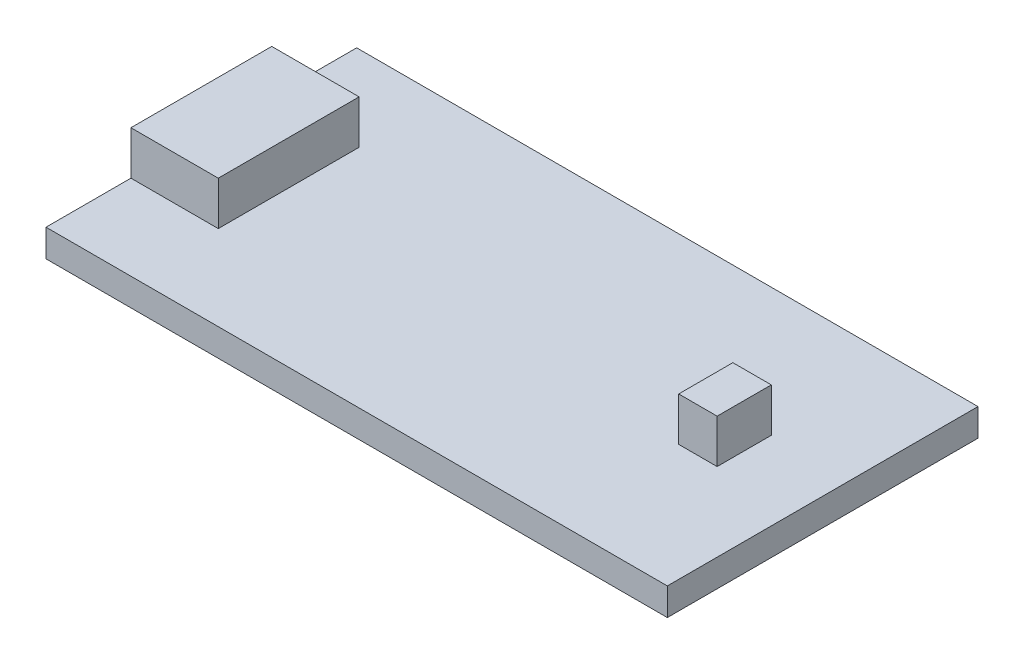
SolidWorks part; units mm, degrees
ref_plane "Front Plane" through (0, 0, 0) normal (0, 0, 1) x (1, 0, 0)
ref_plane "Top Plane" through (0, 0, 0) normal (0, 1, 0) x (1, 0, 0)
ref_plane "Right Plane" through (0, 0, 0) normal (1, 0, 0) x (0, 0, -1)
sketch "Sketch1" plane through (0, 0, 0) normal (0, 1, 0) x (1, 0, 0)
  line L1 (-17.78, 8.89) -> (17.78, 8.89)
  line L2 (-17.78, 8.89) -> (-17.78, -8.89)
  line L3 (-17.78, -8.89) -> (17.78, -8.89)
  line L4 (17.78, 8.89) -> (17.78, -8.89)
  line L5 (0, -8.89) -> (0, 8.89) construction
  line L6 (-17.78, 0) -> (17.78, 0) construction
  point P0 (0, 0)
  dimension "D1" = 35.56
  dimension "D2" = 17.78
extrude "Board" add sketch "Sketch1" along normal blind 1.57
sketch "Sketch2" plane through (0, 1.57, 0) normal (0, 1, 0) x (1, 0, 0)
  line L0 (-17.78, 8.89) -> (-17.78, -8.89) construction
  line L1 (-17.78, -4.03) -> (-12.78, -4.03)
  line L2 (-17.78, -4.03) -> (-17.78, 4.03)
  line L3 (-17.78, 4.03) -> (-12.78, 4.03)
  line L4 (-12.78, -4.03) -> (-12.78, 4.03)
  line L5 (-15.28, 4.03) -> (-15.28, -4.03) construction
  line L6 (-17.78, 0) -> (-12.78, 0) construction
  point P0 (-15.28, 0)
  dimension "D1" = 8.06
  dimension "D2" = 5
extrude "MicroUSB" add sketch "Sketch2" along normal blind 2.5
sketch "Sketch3" plane through (0, 1.57, 0) normal (0, 1, 0) x (1, 0, 0)
  line L0 (-17.78, 8.89) -> (-17.78, 4.03) construction
  line L1 (11.09, -1.55) -> (13.29, -1.55)
  line L2 (11.09, -1.55) -> (11.09, 1.55)
  line L3 (11.09, 1.55) -> (13.29, 1.55)
  line L4 (13.29, -1.55) -> (13.29, 1.55)
  line L5 (12.19, 1.55) -> (12.19, -1.55) construction
  line L6 (11.09, 0) -> (13.29, 0) construction
  point P0 (12.19, 0)
  dimension "D1" = 3.1
  dimension "D2" = 29.97
  dimension "D3" = 2.2
extrude "Button" add sketch "Sketch3" along normal blind 2.5
sketch "Sketch4" plane through (0, 0, 0) normal (0, 1, 0) x (1, 0, 0)
  line L0 (6.4, 8.89) -> (6.4, -8.89) construction
  line L1 (17.78, 8.89) -> (-17.78, 8.89) construction
  line L2 (-17.78, -8.89) -> (17.78, -8.89) construction
  line L3 (17.78, -8.89) -> (17.78, 8.89) construction
  line L4 (-5, 8.89) -> (-5, -8.89) construction
  line L6 (-5, -6.22) -> (6.4, -6.22) construction
  line L7 (-5, -6.22) -> (-5, 5.27) construction
  line L8 (-5, 5.27) -> (6.4, 5.27) construction
  line L9 (6.4, -6.22) -> (6.4, 5.27) construction
  line L10 (-4.0119, 4.9121) -> (-2.6232, 4.9121)
  line L11 (-4.0119, 4.9121) -> (-4.0119, 3.8319)
  line L12 (-4.0119, 3.8319) -> (-2.6232, 3.8319)
  line L13 (-2.6232, 4.9121) -> (-2.6232, 3.8319)
  line L14 (-4.0119, 4.9121) -> (-2.6232, 3.8319) construction
  line L15 (-4.0119, 3.8319) -> (-2.6232, 4.9121) construction
  line L16 (0.7458, 2.5975) -> (1.7745, 2.5975)
  line L17 (0.7458, 2.5975) -> (0.7458, 3.8319)
  line L18 (0.7458, 3.8319) -> (1.7745, 3.8319)
  line L19 (1.7745, 2.5975) -> (1.7745, 3.8319)
  line L20 (0.7458, 2.5975) -> (1.7745, 3.8319) construction
  line L21 (0.7458, 3.8319) -> (1.7745, 2.5975) construction
  line L22 (4.2434, 2.7775) -> (5.375, 2.7775)
  line L23 (4.2434, 2.7775) -> (4.2434, 4.372)
  line L24 (4.2434, 4.372) -> (5.375, 4.372)
  line L25 (5.375, 2.7775) -> (5.375, 4.372)
  line L26 (4.2434, 2.7775) -> (5.375, 4.372) construction
  line L27 (4.2434, 4.372) -> (5.375, 2.7775) construction
  line L28 (3.2404, 1.2344) -> (3.9605, 1.2344)
  line L29 (3.2404, 1.2344) -> (3.2404, -1.2344)
  line L30 (3.2404, -1.2344) -> (3.9605, -1.2344)
  line L31 (3.9605, 1.2344) -> (3.9605, -1.2344)
  line L32 (3.2404, 1.2344) -> (3.9605, -1.2344) construction
  line L33 (3.2404, -1.2344) -> (3.9605, 1.2344) construction
  line L34 (1.1316, -1.8517) -> (-0.6172, -1.8517)
  line L35 (1.1316, -1.8517) -> (1.1316, -3.7033)
  line L36 (1.1316, -3.7033) -> (-0.6172, -3.7033)
  line L37 (-0.6172, -1.8517) -> (-0.6172, -3.7033)
  line L38 (1.1316, -1.8517) -> (-0.6172, -3.7033) construction
  line L39 (1.1316, -3.7033) -> (-0.6172, -1.8517) construction
  line L40 (-2.8546, -2.1367) -> (-3.7805, -2.1367)
  line L41 (-2.8546, -2.1367) -> (-2.8546, -4.5777)
  line L42 (-2.8546, -4.5777) -> (-3.7805, -4.5777)
  line L43 (-3.7805, -2.1367) -> (-3.7805, -4.5777)
  line L44 (-2.8546, -2.1367) -> (-3.7805, -4.5777) construction
  line L45 (-2.8546, -4.5777) -> (-3.7805, -2.1367) construction
  line L46 (-2.7047, 1.163) -> (-1.9388, 1.163)
  line L47 (-2.7047, 1.163) -> (-2.7047, -0.7035)
  line L48 (-2.7047, -0.7035) -> (-1.9388, -0.7035)
  line L49 (-1.9388, 1.163) -> (-1.9388, -0.7035)
  line L50 (-2.7047, 1.163) -> (-1.9388, -0.7035) construction
  line L51 (-2.7047, -0.7035) -> (-1.9388, 1.163) construction
  line L52 (2.7003, -2.8289) -> (3.7805, -2.8289)
  line L53 (2.7003, -2.8289) -> (2.7003, -4.5777)
  line L54 (2.7003, -4.5777) -> (3.7805, -4.5777)
  line L55 (3.7805, -2.8289) -> (3.7805, -4.5777)
  line L56 (2.7003, -2.8289) -> (3.7805, -4.5777) construction
  line L57 (2.7003, -4.5777) -> (3.7805, -2.8289) construction
  point P14 (-3.3176, 4.372)
  point P19 (1.2602, 3.2147)
  point P24 (4.8092, 3.5747)
  point P29 (3.6005, 0)
  point P34 (0.2572, -2.7775)
  point P39 (-3.3176, -3.3572)
  point P44 (-2.3217, 0.2298)
  point P49 (3.2404, -3.7033)
  dimension "D1" = 11.38
  dimension "D2" = 22.78
  dimension "D3" = 3.62
  dimension "D4" = 2.67
extrude "Boss-Extrude1" add sketch "Sketch4" against normal blind 1
